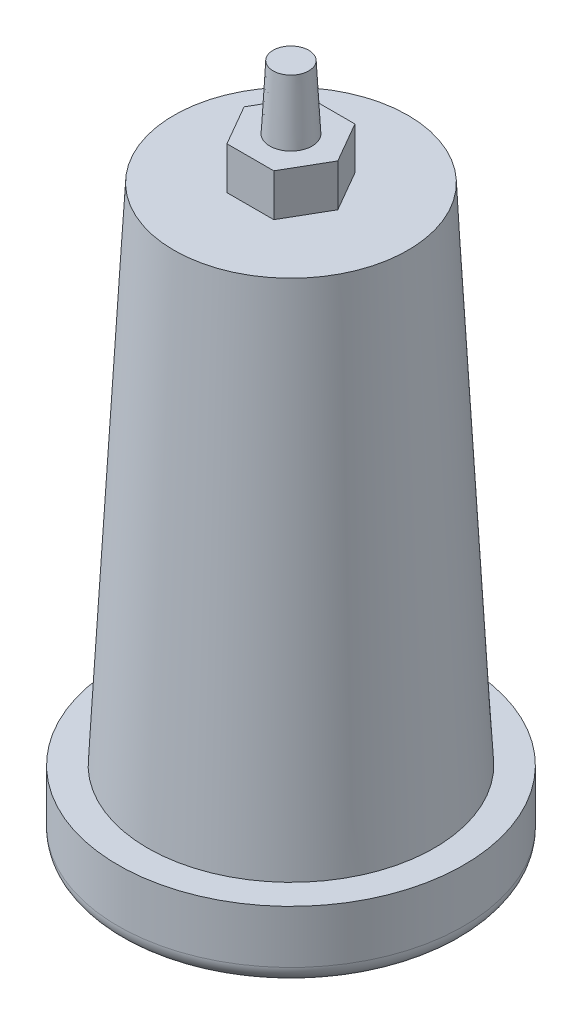
SolidWorks part; units mm, degrees
ref_plane "Front" through (0, 0, 0) normal (0, 0, 1) x (1, 0, 0)
ref_plane "Top" through (0, 0, 0) normal (0, 1, 0) x (1, 0, 0)
ref_plane "Right" through (0, 0, 0) normal (1, 0, 0) x (0, 0, -1)
sketch "Sketch1" plane through (0, 0, 0) normal (0, 1, 0) x (1, 0, 0)
  circle A0 centre (0, 0) radius 40.6566
extrude "Boss-Extrude2" add sketch "Sketch1" along normal blind 143 draft 3
sketch "Sketch2" plane through (0, 0, 0) normal (0, -1, 0) x (-1, 0, 0)
  circle A0 centre (0, 0) radius 49
extrude "Boss-Extrude3" add sketch "Sketch2" along normal blind 20
fillet "Fillet1" radius 5 1 edges at (0, -20, -49)
sketch "Sketch3" plane through (0, 0, 0) normal (0, 1, 0) x (1, 0, 0)
  line L1 (6.6395, -11.5) -> (13.2791, 0)
  line L2 (13.2791, 0) -> (6.6395, 11.5)
  line L3 (6.6395, 11.5) -> (-6.6395, 11.5)
  line L4 (-6.6395, 11.5) -> (-13.2791, 0)
  line L5 (-13.2791, 0) -> (-6.6395, -11.5)
  line L6 (-6.6395, -11.5) -> (6.6395, -11.5)
  circle A0 centre (0, 0) radius 11.5 construction
  dimension "D1" = 23
extrude "Boss-Extrude4" add sketch "Sketch3" along normal blind 12 from surface at 143 starting at face at (0, 143, 33.1623)
sketch "Sketch4" plane through (0, 0, 0) normal (0, 1, 0) x (1, 0, 0)
  circle A0 centre (0, 0) radius 6
  dimension "D1" = 12
extrude "Boss-Extrude5" add sketch "Sketch4" along normal blind 18 draft 3 from surface at 155 starting at face at (0, 155, 0)
